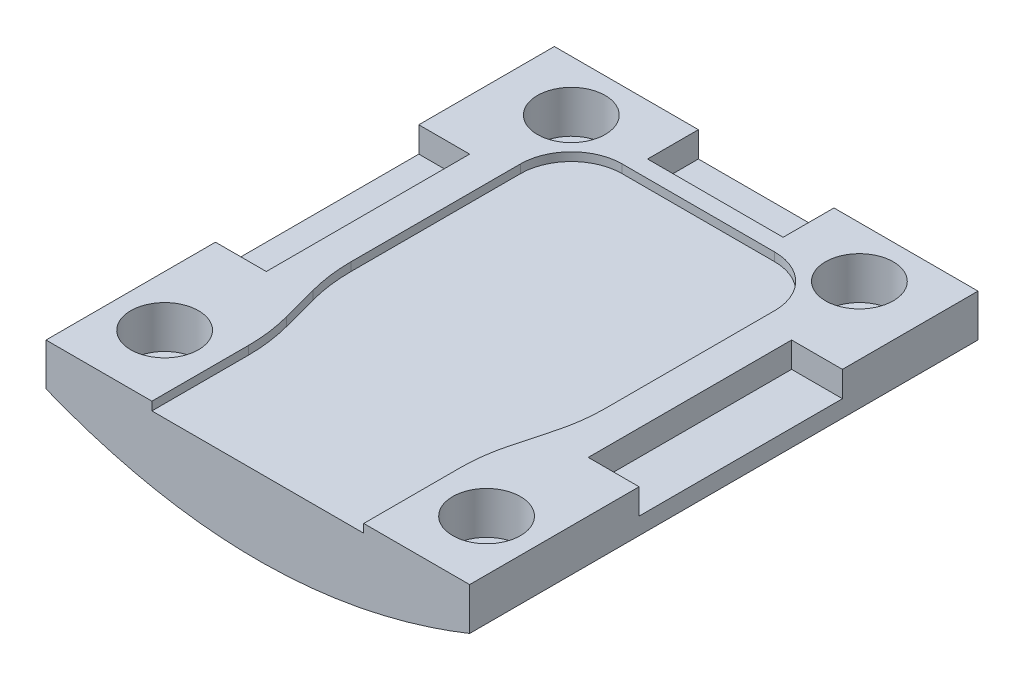
SolidWorks part; units mm, degrees
ref_plane "Front Plane" through (0, 0, 0) normal (0, 0, 1) x (1, 0, 0)
ref_plane "Top Plane" through (0, 0, 0) normal (0, 1, 0) x (1, 0, 0)
ref_plane "Right Plane" through (0, 0, 0) normal (1, 0, 0) x (0, 0, -1)
sketch "Sketch1" plane through (0, 0, 0) normal (0, 1, 0) x (1, 0, 0)
  line L1 (0, 0) -> (25, 0)
  line L2 (0, 0) -> (0, 30)
  line L3 (0, 30) -> (25, 30)
  line L4 (25, 0) -> (25, 30)
  dimension "D1" = 25
  dimension "D2" = 30
extrude "Boss-Extrude1" add sketch "Sketch1" along normal blind 2.5
sketch "Sketch2" plane through (0, 2.5, 0) normal (0, 1, 0) x (1, 0, 0)
  line L0 (25, 0) -> (25, 30) construction
  line L1 (8, 26) -> (17, 26)
  line L2 (5, 23) -> (5, 13)
  line L4 (20, 23) -> (20, 13)
  line L5 (0, 30) -> (0, 0) construction
  line L6 (6.25, 5.6903) -> (6.25, 0)
  line L7 (0, 0) -> (25, 0) construction
  line L8 (18.75, 5.6903) -> (18.75, 0)
  line L11 (19.6627, 10.4248) -> (19.0873, 8.2655)
  line L12 (5.3373, 10.4248) -> (5.9127, 8.2655)
  line L15 (0, 30) -> (0, 0)
  line L16 (0, 0) -> (25, 0)
  line L17 (25, 0) -> (25, 30)
  line L18 (25, 30) -> (0, 30)
  line L20 (6.25, 0) -> (18.75, 0)
  arc A2 (20, 23) -> (17, 26) centre (17, 23) ccw
  arc A3 (8, 26) -> (5, 23) centre (8, 23) ccw
  arc A4 (5.3373, 10.4248) -> (5, 13) centre (15, 13) cw
  arc A5 (5.9127, 8.2655) -> (6.25, 5.6903) centre (-3.75, 5.6903) cw
  arc A6 (19.0873, 8.2655) -> (18.75, 5.6903) centre (28.75, 5.6903) ccw
  arc A7 (19.6627, 10.4248) -> (20, 13) centre (10, 13) ccw
  point P19 (19.5, 25)
  point P21 (6.25, 7)
  point P34 (18.75, 7)
  dimension "D7" = 7
  dimension "D8" = 3
  dimension "D10" = 10
  dimension "D1" = 5
  dimension "D2" = 5
  dimension "D3" = 12.5
  dimension "D4" = 6.25
  dimension "D5" = 7
  dimension "D6" = 26
  dimension "D11" = 10
  dimension "D12" = 10
  dimension "D9" = 0
extrude "Cut-Extrude1" cut sketch "Sketch2" against normal blind 0.5 contours L4 A7 L11 A6 L8 L20 L6 A5 L12 A4 L2 A3 L1 A2
sketch "Sketch3" plane through (0, 2.5, 0) normal (0, 1, 0) x (1, 0, 0)
  line L0 (18.75, 0) -> (25, 0) construction
  line L1 (25, 0) -> (25, 30) construction
  line L2 (0, 0) -> (6.25, 0) construction
  line L3 (0, 30) -> (0, 0) construction
  line L4 (25, 30) -> (0, 30) construction
  circle A0 centre (21, 27) radius 2
  circle A1 centre (4, 27) radius 2
  circle A2 centre (3, 4) radius 2
  circle A3 centre (22, 4) radius 2
  dimension "D1" = 4
  dimension "D2" = 4
  dimension "D3" = 4
  dimension "D4" = 4
  dimension "D5" = 4
  dimension "D6" = 3
  dimension "D7" = 4
  dimension "D8" = 3
  dimension "D9" = 3
  dimension "D10" = 4
  dimension "D11" = 3
  dimension "D12" = 4
extrude "Cut-Extrude2" cut sketch "Sketch3" against normal blind 3.5
sketch "Sketch4" plane through (0, 0, 0) normal (0, 0, 1) x (1, 0, 0)
  line L0 (12.5, 0) -> (12.5, -2.5) construction
  line L1 (0, 0) -> (25, 0) construction
  line L2 (25, 0) -> (0, 0)
  spline S0 degree 2 poles (25, 0) (12.5, -5) (0, 0) knots 0 0 0 1 1 1
  dimension "D1" = 2.5
extrude "Boss-Extrude2" add sketch "Sketch4" against normal blind 30
sketch "Sketch5" plane through (0, 2.5, 0) normal (0, 1, 0) x (1, 0, 0)
  line L0 (25, 30) -> (0, 30) construction
  line L1 (16.5, 30) -> (8.5, 30)
  line L2 (16.5, 30) -> (16.5, 27)
  line L3 (16.5, 27) -> (8.5, 27)
  line L4 (8.5, 30) -> (8.5, 27)
  line L5 (25, 0) -> (25, 30) construction
  line L6 (25, 10) -> (22, 10)
  line L7 (25, 10) -> (25, 22)
  line L8 (25, 22) -> (22, 22)
  line L9 (22, 10) -> (22, 22)
  line L10 (0, 30) -> (0, 0) construction
  line L11 (0, 10) -> (3, 10)
  line L12 (0, 10) -> (0, 22)
  line L13 (0, 22) -> (3, 22)
  line L14 (3, 10) -> (3, 22)
  dimension "D1" = 3
  dimension "D2" = 12
  dimension "D3" = 8
  dimension "D4" = 8
  dimension "D5" = 12
  dimension "D6" = 8
  dimension "3" = 3
  dimension "D7" = 3
  dimension "D8" = 8.5
extrude "Cut-Extrude3" cut sketch "Sketch5" against normal blind 1.5
